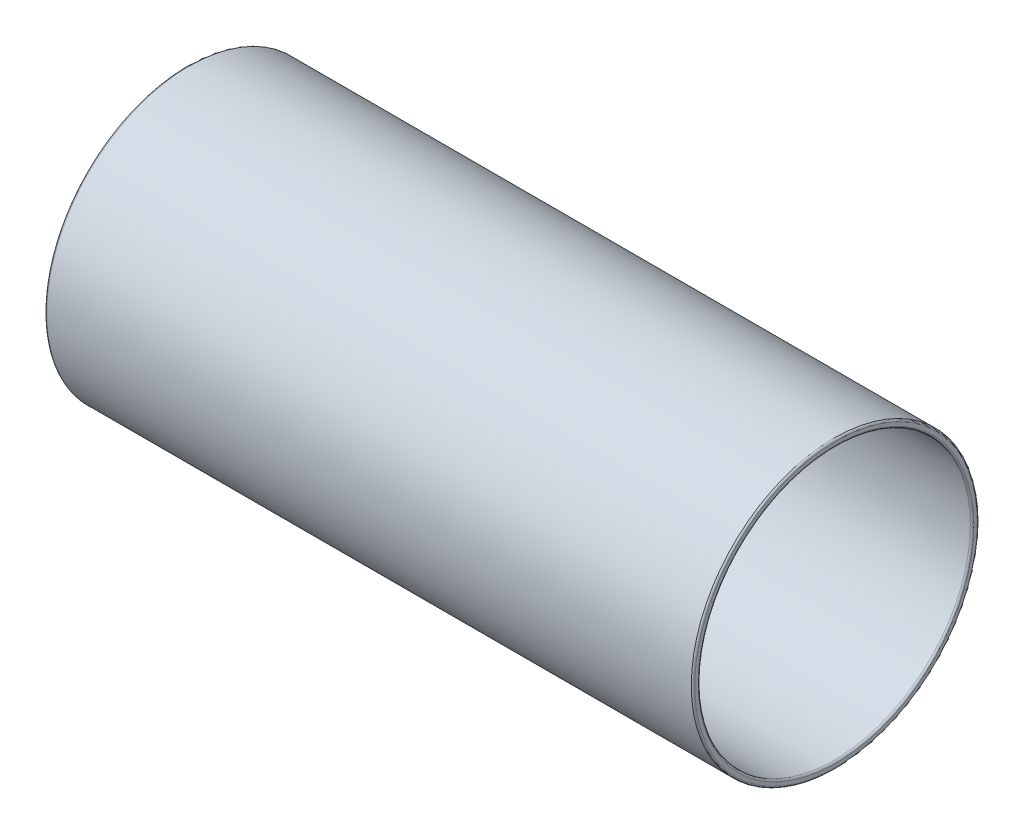
SolidWorks part; units mm, degrees
ref_plane "Front Plane" through (0, 0, 0) normal (0, 0, 1) x (1, 0, 0)
ref_plane "Top Plane" through (0, 0, 0) normal (0, 1, 0) x (1, 0, 0)
ref_plane "Right Plane" through (0, 0, 0) normal (1, 0, 0) x (0, 0, -1)
sketch "Sketch1" plane through (0, 0, 0) normal (1, 0, 0) x (0, 0, -1)
  circle A0 centre (0, 0) radius 165.5
extrude "Boss-Extrude1" add sketch "Sketch1" against normal blind 750
sketch "Sketch2" plane through (0, 0, 0) normal (1, 0, 0) x (0, 0, -1)
  circle A0 centre (0, 0) radius 157.5
  circle A1 centre (0, 0) radius 165.5 construction
  dimension "D1" = 8
extrude "Cut-Extrude1" cut sketch "Sketch2" against normal blind 750
fillet "Fillet1" radius 2 2 edges at (0, 0, -165.5) (0, 0, -157.5)
fillet "Fillet2" radius 2 2 edges at (-750, 0, -165.5) (-750, 0, -157.5)
